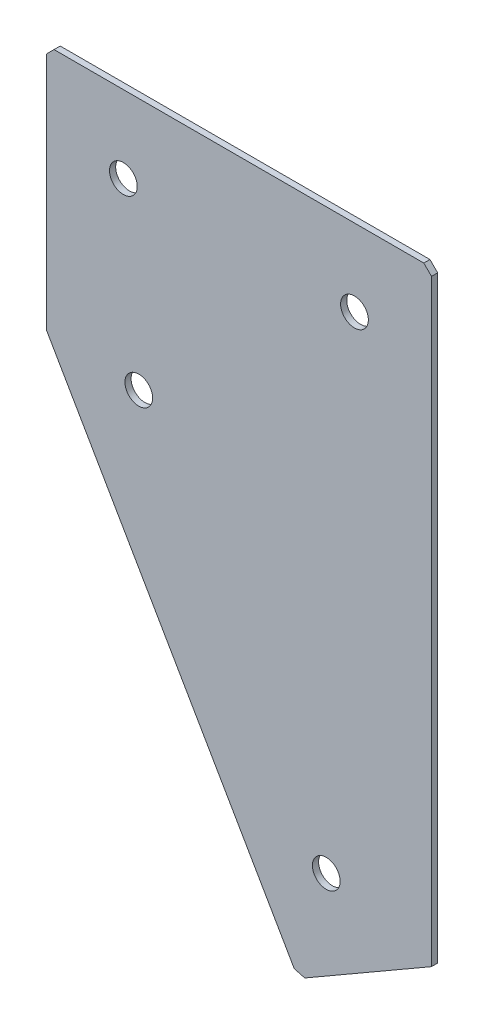
SolidWorks part; units mm, degrees
material "Простая углеродистая сталь"
ref_plane "Спереди" through (0, 0, 0) normal (0, 0, 1) x (1, 0, 0)
ref_plane "Сверху" through (0, 0, 0) normal (0, 1, 0) x (1, 0, 0)
ref_plane "Справа" through (0, 0, 0) normal (1, 0, 0) x (0, 0, -1)
sketch "Эскиз3" plane through (0, 0, 0) normal (0, 0, -1) x (1, 0, 0)
  line L0 (0, 0) -> (125, 0)
  line L1 (125, 0) -> (125, 196.5064)
  line L2 (0, 0) -> (0, 80)
  line L3 (0, 80) -> (81.6987, 221.5064)
  line L4 (81.6987, 221.5064) -> (125, 196.5064)
  dimension "D1" = 125
  dimension "D2" = 80
  dimension "D3" = 50
  dimension "D4" = 60
  dimension "D5" = 196.5064
extrude "Бобышка-Вытянуть1" add sketch "Эскиз3" along normal blind 2
hole_wizard "Отверстие с зазором M81" positions "Эскиз4" profile "Эскиз5" hole size "M8" standard "DIN" end condition through all
sketch "Эскиз4" plane through (0, 0, -2) normal (0, 0, -1) x (1, 0, 0)
  line L0 (30, 81.9615) -> (90.8494, 187.3557) construction
  line L2 (81.6987, 221.5064) -> (0, 80) construction
  line L3 (25, 25) -> (100, 25) construction
  line L5 (0, 0) -> (125, 0) construction
  line L6 (0, 80) -> (0, 0) construction
  line L7 (125, 0) -> (125, 196.5064) construction
  line L8 (125, 196.5064) -> (81.6987, 221.5064) construction
  line L9 (30, 81.9615) -> (0, 30) construction
  point P0 (25, 25)
  point P2 (100, 25)
  point P4 (30, 81.9615)
  point P6 (90.8494, 187.3557)
  dimension "D1" = 25
  dimension "D2" = 25
  dimension "D3" = 25
  dimension "D4" = 25
  dimension "D5" = 25
  dimension "D6" = 60
  dimension "D7" = 121.6987
  dimension "D8" = 75
sketch "Эскиз5" plane through (25, -25, -2) normal (1, 0, 0) x (0, 1, 0)
  line L0 (0, 0) -> (0, 2)
  line L1 (0, 2) -> (4.5, 2)
  line L2 (4.5, 2) -> (4.5, 0)
  line L5 (4.5, 0) -> (0, 0)
  line L11 (0, -6.35) -> (0, 107.95) construction
  dimension "Диаметр сквозного отверстия" = 9
  dimension "Глубина сквозного отверстия" = 2
chamfer "Фаска1" distance 2.5 distance2 2.5 3 edges at (81.6987, -221.5064, -1) (125, 0, -1) (0, 0, -1)
